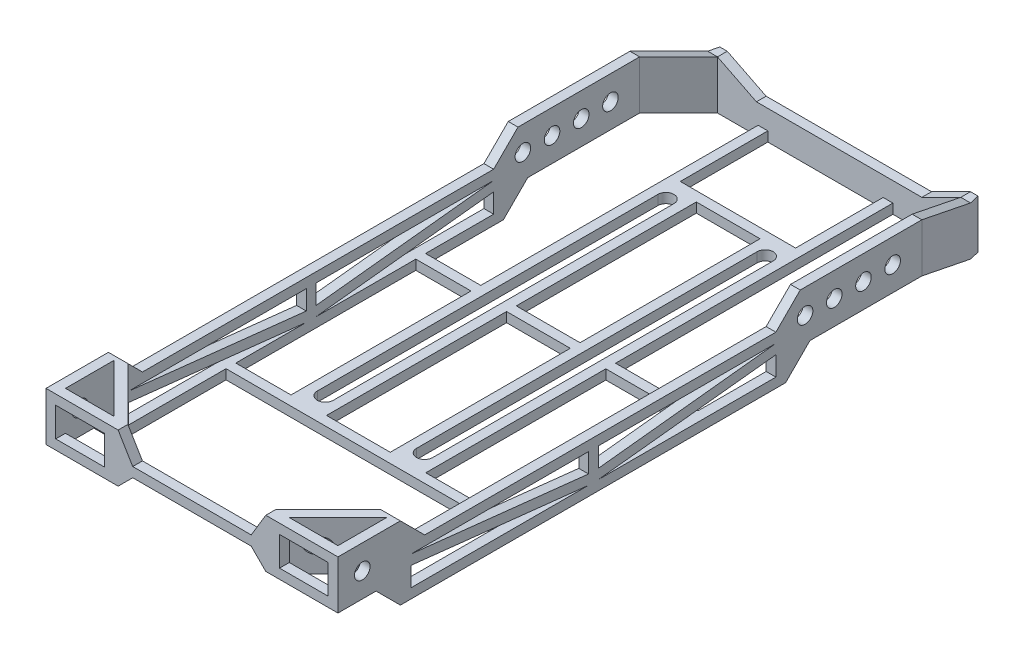
SolidWorks part; units mm, degrees
ref_plane "Front Plane" through (0, 0, 0) normal (0, 0, 1) x (1, 0, 0)
ref_plane "Top Plane" through (0, 0, 0) normal (0, 1, 0) x (1, 0, 0)
ref_plane "Right Plane" through (0, 0, 0) normal (1, 0, 0) x (0, 0, -1)
sketch "Sketch1" plane through (0, 0, 0) normal (0, 1, 0) x (1, 0, 0)
  line L0 (38.1, -76.2) -> (38.1, 76.2)
  line L1 (-38.1, 76.2) -> (-35.56, 76.2)
  line L2 (-38.1, 76.2) -> (-38.1, -76.2)
  line L3 (-38.1, -76.2) -> (38.1, -76.2)
  line L4 (35.56, 76.2) -> (35.56, -57.3679)
  line L5 (-38.1, 76.2) -> (38.1, -76.2) construction
  line L6 (-38.1, -76.2) -> (38.1, 76.2) construction
  line L8 (-35.56, -73.66) -> (-22.86, -73.66)
  line L9 (-38.1, 76.2) -> (-38.1, -76.2) construction
  line L11 (-35.56, -60.96) -> (-22.86, -73.66)
  line L12 (22.86, -73.66) -> (35.56, -60.96)
  line L14 (-35.56, 76.2) -> (-35.56, -57.3679)
  line L15 (35.56, -57.3679) -> (19.2679, -73.66)
  line L16 (-35.56, -57.3679) -> (-19.2679, -73.66)
  line L17 (38.1, 76.2) -> (35.56, 76.2)
  line L19 (38.1, 76.2) -> (38.1, -76.2) construction
  line L20 (-35.56, 73.66) -> (-35.56, -73.66) construction
  line L21 (35.56, 73.66) -> (35.56, -73.66) construction
  line L22 (-35.56, 73.66) -> (35.56, 73.66) construction
  line L25 (35.56, -60.96) -> (35.56, -73.66)
  line L26 (22.86, -73.66) -> (35.56, -73.66)
  line L27 (-19.2679, -73.66) -> (19.2679, -73.66)
  line L28 (-35.56, -73.66) -> (35.56, -73.66) construction
  line L29 (-35.56, -60.96) -> (-35.56, -73.66)
  line L35 (-38.1, 76.2) -> (38.1, 76.2) construction
  point P0 (0, 0)
  dimension "D1" = 152.4
  dimension "D2" = 76.2
  dimension "D7" = 12.7
  dimension "D8" = 12.7
  dimension "D9" = 12.7
  dimension "D10" = 76.2
  dimension "D11" = 2.54
  dimension "D12" = 2.54
  dimension "D3" = 2.54
extrude "Boss-Extrude1" add sketch "Sketch1" along normal blind 12.7
sketch "Sketch7" plane through (38.1, 0, 0) normal (1, 0, 0) x (0, 0, -1)
  line L0 (-76.2, 0) -> (76.2, 0) construction
  line L2 (-76.2, 12.7) -> (-76.2, 0) construction
  line L3 (-76.2, 12.7) -> (76.2, 12.7) construction
  line L4 (-57.15, 10.16) -> (-10.7951, 10.16)
  line L5 (-57.15, 7.6049) -> (-57.15, 2.54)
  line L6 (-57.15, 2.54) -> (-10.795, 2.54)
  line L7 (-10.7951, 10.16) -> (-10.7951, 5.0951)
  line L8 (-8.2551, 10.16) -> (38.1, 10.16)
  line L9 (-8.2551, 10.16) -> (-8.2551, 5.0951)
  line L10 (-8.255, 2.54) -> (38.1, 2.54)
  line L11 (38.1, 7.6049) -> (38.1, 2.54)
  line L12 (-57.15, 10.16) -> (-10.7951, 5.0951)
  line L13 (-10.795, 2.54) -> (-57.15, 7.6049)
  line L14 (-8.255, 2.54) -> (38.1, 7.6049)
  line L15 (-8.2551, 5.0951) -> (38.1, 10.16)
  line L18 (76.2, 12.7) -> (76.2, 0) construction
  dimension "D7" = 19.05
  dimension "D8" = 38.1
  dimension "D9" = 38.1
  dimension "D10" = 2.54
  dimension "D11" = 2.54
  dimension "D12" = 2.54
  dimension "D13" = 2.54
  dimension "D14" = 2.54
  dimension "D15" = 2.54
  dimension "D16" = 2.54
  dimension "D19" = 46.355
  dimension "D25" = 2.54
  dimension "D26" = 19.05
extrude "Cut-Extrude3" cut sketch "Sketch7" against normal through all
sketch "Sketch8" plane through (0, 0, 0) normal (0, -1, 0) x (1, 0, 0)
  line L0 (-35.56, 57.3679) -> (-35.56, -76.2) construction
  line L1 (-35.56, -69.85) -> (35.56, -69.85)
  line L2 (-35.56, -69.85) -> (-35.56, 31.75)
  line L3 (-35.56, 31.75) -> (35.56, 31.75)
  line L4 (35.56, -69.85) -> (35.56, 31.75)
  line L5 (35.56, -76.2) -> (35.56, 57.3679) construction
  line L6 (-35.56, -76.2) -> (-38.1, -76.2) construction
  dimension "D1" = 101.6
  dimension "D2" = 6.35
extrude "Boss-Extrude3" add sketch "Sketch8" against normal blind 2.54
sketch "Sketch9" plane through (0, 2.54, 0) normal (0, 1, 0) x (1, 0, 0)
  line L0 (-35.56, 69.85) -> (-35.56, -29.21)
  line L1 (-21.1455, -29.21) -> (-21.1455, 69.85)
  line L2 (-14.4145, 64.008) -> (-14.4145, -24.892)
  line L3 (-18.6055, -24.892) -> (-18.6055, 64.008)
  line L4 (35.56, -31.75) -> (-35.56, -31.75) construction
  line L5 (-35.56, 69.85) -> (-21.1455, 69.85)
  line L6 (35.56, 20.32) -> (35.56, 69.85)
  line L7 (-11.8745, 67.31) -> (4.7625, 67.31)
  line L8 (7.3025, 64.008) -> (7.3025, -24.892)
  line L9 (11.4935, 64.008) -> (11.4935, -24.892)
  line L10 (-35.56, 69.85) -> (35.56, 69.85) construction
  line L11 (-11.8745, 67.31) -> (-11.8745, 20.32)
  line L12 (-11.8745, -29.21) -> (4.7625, -29.21)
  line L13 (4.7625, 67.31) -> (4.7625, 20.32)
  line L14 (35.56, 20.32) -> (14.0335, 20.32)
  line L15 (35.56, 69.85) -> (14.0335, 69.85)
  line L16 (35.56, 17.78) -> (14.0335, 17.78)
  line L17 (-35.56, -29.21) -> (-21.1455, -29.21)
  line L18 (4.7625, 17.78) -> (4.7625, -29.21)
  line L19 (14.0335, -29.21) -> (35.56, -29.21)
  line L20 (14.0335, -29.21) -> (14.0335, 17.78)
  line L21 (14.0335, 69.85) -> (14.0335, 20.32)
  line L22 (35.56, -29.21) -> (35.56, 17.78)
  line L23 (4.7625, 17.78) -> (-11.8745, 17.78)
  line L24 (-11.8745, 17.78) -> (-11.8745, -29.21)
  line L25 (4.7625, 20.32) -> (-11.8745, 20.32)
  arc A0 (-14.4145, 64.008) -> (-18.6055, 64.008) centre (-16.51, 64.008) ccw
  arc A1 (11.4935, 64.008) -> (7.3025, 64.008) centre (9.398, 64.008) ccw
  arc A3 (11.4935, -24.892) -> (7.3025, -24.892) centre (9.398, -24.892) cw
  arc A5 (-14.4145, -24.892) -> (-18.6055, -24.892) centre (-16.51, -24.892) cw
  dimension "D4" = 5.842
  dimension "D6" = 4.191
  dimension "D7" = 2.54
  dimension "D8" = 4.191
  dimension "D1" = 88.9
  dimension "D2" = 25.908
  dimension "D3" = 19.05
  dimension "D5" = 2.54
  dimension "D9" = 88.9
  dimension "D10" = 5.842
  dimension "D11" = 2.54
  dimension "D12" = 2.54
  dimension "D13" = 2.54
  dimension "D14" = 2.54
  dimension "D15" = 21.5265
  dimension "D16" = 46.99
  dimension "D17" = 2.54
  dimension "D18" = 21.5265
  dimension "D19" = 2.54
  dimension "D20" = 2.54
  dimension "D21" = 46.99
  dimension "D22" = 14.4145
  dimension "D23" = 2.54
extrude "Cut-Extrude4" cut sketch "Sketch9" against normal blind 2.54
sketch "Sketch16" plane through (0, 0, 0) normal (0, -1, 0) x (1, 0, 0)
  line L0 (-35.56, -76.2) -> (-31.75, -92.71)
  line L1 (-31.75, -92.71) -> (31.75, -92.71)
  line L2 (31.75, -92.71) -> (35.56, -76.2)
  line L3 (-38.1, -76.2) -> (-33.7038, -95.25)
  line L4 (-33.7038, -95.25) -> (33.7038, -95.25)
  line L5 (33.7038, -95.25) -> (38.1, -76.2)
  line L6 (-38.1, -76.2) -> (-35.56, -76.2)
  line L7 (38.1, -76.2) -> (35.56, -76.2)
  dimension "D1" = 16.51
  dimension "D2" = 3.81
  dimension "D3" = 3.81
  dimension "D4" = 2.54
extrude "Boss-Extrude4" add sketch "Sketch16" against normal blind 12.7
sketch "Sketch19" plane through (0, 0, -69.85) normal (0, 0, -1) x (-1, 0, 0)
  line L0 (21.1455, 0) -> (-14.0335, 0) construction
  line L1 (21.1455, 2.54) -> (18.6055, 2.54)
  line L2 (21.1455, 2.54) -> (21.1455, 0)
  line L3 (21.1455, 0) -> (18.6055, 0)
  line L4 (18.6055, 2.54) -> (18.6055, 0)
  line L5 (21.1455, 0) -> (-14.0335, 0) construction
  line L6 (-14.0335, 2.54) -> (-11.4935, 2.54)
  line L7 (-14.0335, 2.54) -> (-14.0335, 0)
  line L8 (-14.0335, 0) -> (-11.4935, 0)
  line L9 (-11.4935, 2.54) -> (-11.4935, 0)
  dimension "D1" = 2.54
  dimension "D2" = 2.54
extrude "Boss-Extrude6" add sketch "Sketch19" along normal blind 25.4
sketch "Sketch21" plane through (0, 12.7, 0) normal (0, 1, 0) x (1, 0, 0)
  line L0 (38.1, 38.1) -> (38.1, 76.2)
  line L1 (35.56, 38.1) -> (38.1, 38.1)
  line L2 (35.56, 76.2) -> (35.56, -57.3679) construction
  line L3 (38.1, -76.2) -> (38.1, 76.2) construction
  line L4 (38.1, 76.2) -> (33.7038, 95.25)
  line L5 (33.7038, 95.25) -> (31.75, 92.71)
  line L6 (31.75, 92.71) -> (35.56, 76.2)
  line L7 (35.56, 76.2) -> (35.56, 38.1)
  line L8 (-35.56, 38.1) -> (-38.1, 38.1)
  line L9 (-35.56, -57.3679) -> (-35.56, 76.2) construction
  line L10 (-38.1, 76.2) -> (-38.1, -76.2) construction
  line L11 (-31.75, 92.71) -> (-35.56, 76.2)
  line L12 (-31.75, 92.71) -> (-33.7038, 95.25)
  line L13 (-35.56, 76.2) -> (-35.56, 38.1)
  line L14 (-38.1, 38.1) -> (-38.1, 76.2)
  line L15 (-38.1, 76.2) -> (-33.7038, 95.25)
  dimension "D1" = 38.1
extrude "Boss-Extrude7" add sketch "Sketch21" along normal blind 6.35
sketch "Sketch24" plane through (0, 12.7, 0) normal (0, 1, 0) x (1, 0, 0)
  line L1 (-38.1, 38.1) -> (-38.1, -76.2) construction
  line L2 (-38.1, -57.3679) -> (-38.1, -76.2)
  line L3 (-38.1, -76.2) -> (-19.2679, -76.2)
  line L4 (-38.1, -76.2) -> (38.1, -76.2) construction
  line L6 (-19.2679, -73.66) -> (-35.56, -57.3679)
  line L8 (19.2679, -76.2) -> (38.1, -76.2)
  line L9 (38.1, -76.2) -> (38.1, -57.3679)
  line L10 (38.1, -76.2) -> (38.1, 38.1) construction
  line L12 (35.56, -57.3679) -> (19.2679, -73.66)
  line L13 (22.86, -73.66) -> (35.56, -60.96)
  line L14 (35.56, -60.96) -> (35.56, -73.66)
  line L15 (35.56, -73.66) -> (22.86, -73.66)
  line L16 (-22.86, -73.66) -> (-35.56, -60.96)
  line L17 (-35.56, -60.96) -> (-35.56, -73.66)
  line L18 (-35.56, -73.66) -> (-22.86, -73.66)
  line L20 (-19.2679, -73.66) -> (-15.4579, -73.66)
  line L22 (-19.2679, -76.2) -> (-15.4579, -76.2)
  line L23 (-15.4579, -73.66) -> (-15.4579, -76.2)
  line L24 (19.2679, -73.66) -> (15.4579, -73.66)
  line L26 (19.2679, -76.2) -> (15.4579, -76.2)
  line L27 (15.4579, -73.66) -> (15.4579, -76.2)
  line L29 (35.56, -57.3679) -> (35.56, -53.5579)
  line L30 (35.56, -53.5579) -> (38.1, -53.5579)
  line L31 (38.1, -57.3679) -> (38.1, -53.5579)
  line L33 (-35.56, -57.3679) -> (-35.56, -53.5579)
  line L34 (-35.56, -53.5579) -> (-38.1, -53.5579)
  line L35 (-38.1, -57.3679) -> (-38.1, -53.5579)
  dimension "D1" = 3.81
  dimension "D2" = 3.81
  dimension "D3" = 3.81
  dimension "D4" = 3.81
extrude "Boss-Extrude8" add sketch "Sketch24" along normal blind 6.35
sketch "Sketch26" plane through (38.1, 0, 0) normal (1, 0, 0) x (0, 0, -1)
  line L0 (-53.5579, 12.7) -> (-59.9079, 19.05)
  line L1 (-76.2, 19.05) -> (-53.5579, 19.05) construction
  line L2 (-59.9079, 19.05) -> (-53.5579, 19.05)
  line L3 (-53.5579, 19.05) -> (-53.5579, 12.7)
  line L4 (-59.9079, 0) -> (-66.2579, 6.35)
  line L5 (-76.2, 0) -> (76.2, 0) construction
  line L6 (-66.2579, 6.35) -> (-76.2, 6.35)
  line L7 (-76.2, 19.05) -> (-76.2, 0) construction
  line L8 (-76.2, 6.35) -> (-76.2, 0)
  line L9 (-76.2, 0) -> (-59.9079, 0)
  dimension "D1" = 6.35
  dimension "D2" = 6.35
  dimension "D3" = 6.35
extrude "Cut-Extrude9" cut sketch "Sketch26" against normal through all
sketch "Sketch27" plane through (0, 0, 76.2) normal (0, 0, 1) x (1, 0, 0)
  line L0 (-15.4579, 12.7) -> (-19.2679, 19.05)
  line L1 (-38.1, 19.05) -> (-15.4579, 19.05) construction
  line L2 (-19.2679, 19.05) -> (-15.4579, 19.05)
  line L3 (-15.4579, 19.05) -> (-15.4579, 12.7)
  line L4 (15.4579, 12.7) -> (15.4579, 19.05)
  line L5 (15.4579, 19.05) -> (19.2679, 19.05)
  line L6 (15.4579, 19.05) -> (38.1, 19.05) construction
  line L7 (19.2679, 19.05) -> (15.4579, 12.7)
  line L8 (-19.2679, 6.35) -> (-15.4579, 10.16)
  line L9 (-38.1, 6.35) -> (38.1, 6.35) construction
  line L10 (-15.4579, 10.16) -> (15.4579, 10.16)
  line L11 (15.4579, 10.16) -> (19.2679, 6.35)
  line L12 (-19.2679, 6.35) -> (19.2679, 6.35)
  dimension "D1" = 3.81
  dimension "D2" = 3.81
  dimension "D3" = 3.81
  dimension "D4" = 3.81
  dimension "D5" = 3.81
extrude "Cut-Extrude10" cut sketch "Sketch27" against normal blind 2.54
sketch "Sketch28" plane through (0, 0, 76.2) normal (0, 0, 1) x (1, 0, 0)
  line L0 (-38.1, 19.05) -> (-38.1, 6.35) construction
  line L1 (-35.56, 16.51) -> (-22.86, 16.51)
  line L2 (-35.56, 16.51) -> (-35.56, 8.89)
  line L3 (-35.56, 8.89) -> (-22.86, 8.89)
  line L4 (-22.86, 16.51) -> (-22.86, 8.89)
  line L5 (35.56, 16.51) -> (22.86, 16.51)
  line L6 (35.56, 16.51) -> (35.56, 8.89)
  line L7 (35.56, 8.89) -> (22.86, 8.89)
  line L8 (38.1, 19.05) -> (38.1, 6.35) construction
  line L9 (-38.1, 19.05) -> (-19.2679, 19.05) construction
  line L11 (22.86, 16.51) -> (22.86, 8.89)
  line L15 (-38.1, 6.35) -> (-19.2679, 6.35) construction
  line L16 (19.2679, 19.05) -> (38.1, 19.05) construction
  line L17 (19.2679, 6.35) -> (38.1, 6.35) construction
  point P10 (-28.6839, 19.05)
  dimension "D1" = 2.54
  dimension "D2" = 2.54
  dimension "D3" = 12.7
  dimension "D4" = 12.7
  dimension "D5" = 2.54
  dimension "D6" = 12.7
  dimension "D7" = 12.7
  dimension "D8" = 2.54
  dimension "D9" = 2.54
  dimension "D10" = 2.54
extrude "Cut-Extrude11" cut sketch "Sketch28" against normal blind 2.54
sketch "Sketch29" plane through (38.1, 0, 0) normal (1, 0, 0) x (0, 0, -1)
  line L0 (38.1, 12.7) -> (44.45, 19.05)
  line L1 (38.1, 19.05) -> (76.2, 19.05) construction
  line L2 (44.45, 19.05) -> (38.1, 19.05)
  line L3 (38.1, 19.05) -> (38.1, 12.7)
  line L4 (40.64, 0) -> (46.99, 6.35)
  line L5 (-59.9079, 0) -> (76.2, 0) construction
  line L6 (46.99, 6.35) -> (76.2, 6.35)
  line L7 (76.2, 19.05) -> (76.2, 0) construction
  line L8 (76.2, 6.35) -> (92.71, 0)
  line L9 (95.25, 0) -> (76.2, 0) construction
  line L10 (92.71, 0) -> (40.64, 0)
  line L11 (76.2, 19.05) -> (92.71, 12.7)
  line L12 (92.71, 12.7) -> (95.25, 12.7)
  line L13 (95.25, 12.7) -> (95.25, 0) construction
  line L14 (95.25, 12.7) -> (95.25, 19.05)
  line L15 (95.25, 19.05) -> (76.2, 19.05)
  dimension "D1" = 6.35
  dimension "D2" = 6.35
  dimension "D3" = 6.35
  dimension "D4" = 16.51
  dimension "D5" = 16.51
  dimension "D6" = 6.35
  dimension "D7" = 29.21
extrude "Cut-Extrude12" cut sketch "Sketch29" against normal blind 12.7
sketch "Sketch30" plane through (-38.1, 0, 0) normal (-1, 0, 0) x (0, 0, 1)
  line L0 (-38.1, 12.7) -> (-44.45, 19.05)
  line L1 (-76.2, 19.05) -> (-38.1, 19.05) construction
  line L2 (-44.45, 19.05) -> (-38.1, 19.05)
  line L3 (-38.1, 19.05) -> (-38.1, 12.7)
  line L4 (-46.99, 6.35) -> (-40.64, 0)
  line L6 (-46.99, 6.35) -> (-76.2, 6.35)
  line L7 (-76.2, 19.05) -> (-76.2, 0) construction
  line L8 (-76.2, 6.35) -> (-92.71, 0)
  line L9 (-76.2, 0) -> (-95.25, 0) construction
  line L10 (-76.2, 0) -> (59.9079, 0) construction
  line L11 (-76.2, 19.05) -> (-92.71, 12.7)
  line L12 (-92.71, 12.7) -> (-95.25, 12.7)
  line L13 (-95.25, 12.7) -> (-95.25, 19.05)
  line L14 (-95.25, 19.05) -> (-76.2, 19.05)
  line L15 (-40.64, 0) -> (-92.71, 0)
  dimension "D1" = 6.35
  dimension "D2" = 16.51
  dimension "D3" = 16.51
  dimension "D4" = 6.35
  dimension "D5" = 29.21
  dimension "D6" = 6.35
extrude "Cut-Extrude13" cut sketch "Sketch30" against normal blind 12.7
sketch "Sketch32" plane through (38.1, 0, 0) normal (1, 0, 0) x (0, 0, -1)
  line L0 (-76.2, 19.05) -> (-76.2, 6.35) construction
  line L1 (-66.2579, 6.35) -> (-76.2, 6.35) construction
  line L2 (76.2, 6.35) -> (46.99, 6.35) construction
  line L3 (38.1, 2.54) -> (38.1, 7.6049) construction
  circle A0 centre (45.72, 12.7) radius 2.032
  circle A1 centre (53.34, 12.7) radius 2.032
  circle A2 centre (60.96, 12.7) radius 2.032
  circle A3 centre (68.58, 12.7) radius 2.032
  circle A4 centre (-69.85, 12.7) radius 2.032
  point P10 (-76.2, 12.7)
  dimension "D3" = 4.064
  dimension "D4" = 4.064
  dimension "D5" = 4.064
  dimension "D6" = 4.064
  dimension "D7" = 4.064
  dimension "D1" = 6.35
  dimension "D2" = 6.35
  dimension "D8" = 6.35
  dimension "D9" = 6.35
  dimension "D10" = 6.35
  dimension "D11" = 6.35
  dimension "D12" = 7.62
  dimension "D13" = 7.62
  dimension "D14" = 7.62
  dimension "D15" = 7.62
extrude "Cut-Extrude15" cut sketch "Sketch32" against normal through all
sketch "Sketch33" plane through (-21.1455, 0, 0) normal (-1, 0, 0) x (0, 0, 1)
  line L0 (29.21, 2.54) -> (-92.71, 2.54) construction
  line L1 (-20.32, 2.54) -> (-17.78, 2.54)
  line L2 (-20.32, 2.54) -> (-20.32, 0)
  line L3 (-20.32, 0) -> (-17.78, 0)
  line L4 (-17.78, 2.54) -> (-17.78, 0)
  line L5 (29.21, 0) -> (-92.71, 0) construction
  line L6 (29.21, 0) -> (29.21, 2.54) construction
  dimension "D1" = 2.54
  dimension "D2" = 46.99
extrude "Boss-Extrude9" add sketch "Sketch33" along normal blind 15.24
sketch "Sketch35" plane through (0, 0, -92.71) normal (0, 0, 1) x (1, 0, 0)
  line L0 (-31.75, 12.7) -> (-21.59, 7.62)
  line L1 (-21.59, 7.62) -> (21.59, 7.62)
  line L2 (21.59, 7.62) -> (31.75, 12.7)
  line L3 (11.4935, 2.54) -> (14.0335, 2.54) construction
  line L5 (-31.75, 12.7) -> (31.75, 12.7)
  dimension "D1" = 5.08
  dimension "D2" = 10.16
  dimension "D3" = 10.16
extrude "Cut-Extrude17" cut sketch "Sketch35" against normal blind 2.54
